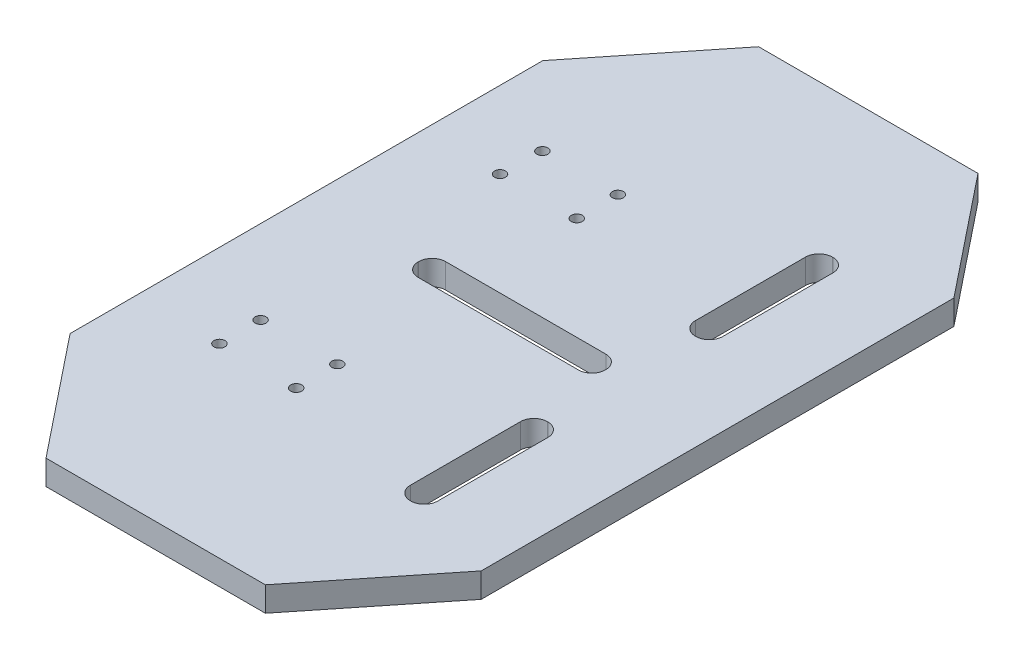
SolidWorks part; units mm, degrees
material "ABS"
ref_plane "Front Plane" through (0, 0, 0) normal (0, 0, 1) x (1, 0, 0)
ref_plane "Top Plane" through (0, 0, 0) normal (0, 1, 0) x (1, 0, 0)
ref_plane "Right Plane" through (0, 0, 0) normal (1, 0, 0) x (0, 0, -1)
other "Center of Mass"
sketch "Sketch1" plane through (0, 0, 0) normal (0, 1, 0) x (1, 0, 0)
  line L0 (-37.5, -43.1177) -> (-20.0119, -65)
  line L1 (-20.0119, -65) -> (20.0119, -65)
  line L2 (-37.5, -43.1177) -> (-37.5, 43.1177)
  line L3 (-20.0119, 65) -> (20.0119, 65)
  line L4 (37.5, -43.1177) -> (37.5, 43.1177)
  line L5 (-30.8066, -51.493) -> (30.8066, 51.493) construction
  line L6 (-32.7951, 49.0048) -> (32.7951, -49.0048) construction
  line L7 (-114.8204, 0) -> (150.9847, 0) construction
  line L8 (0, -72.5189) -> (0, 84.1411) construction
  line L9 (37.5, -43.1177) -> (20.0119, -65)
  line L10 (37.5, 43.1177) -> (20.0119, 65)
  line L11 (-37.5, 43.1177) -> (-20.0119, 65)
  point P0 (0, 0)
  dimension "D1" = 75
  dimension "D2" = 130
  dimension "D3" = 40.0238
  dimension "D4" = 86.2354
extrude "Boss-Extrude1" add sketch "Sketch1" along normal blind 4.5
sketch "Sketch5" plane through (0, 4.5, 0) normal (0, 1, 0) x (1, 0, 0)
  line L0 (-100.8141, 0) -> (111.641, 0) construction
  line L1 (20, 65) -> (20, -65) construction
  line L2 (-14.6202, -2.5) -> (14.6202, -2.5)
  line L3 (-17.0702, -0.05) -> (-17.0702, 0.05)
  line L4 (-14.6202, 2.5) -> (14.6202, 2.5)
  line L5 (17.0702, -0.05) -> (17.0702, 0.05)
  line L6 (-17.0702, -2.5) -> (17.0702, 2.5) construction
  line L7 (-17.0702, 2.5) -> (17.0702, -2.5) construction
  line L8 (20.0119, 65) -> (-20.0119, 65) construction
  line L9 (-20.0119, -65) -> (20.0119, -65) construction
  line L10 (20, 65) -> (20, 0) construction
  line L11 (20, 0) -> (20, -65) construction
  line L12 (19.95, -38.5) -> (20.05, -38.5)
  line L13 (19.95, 13.5) -> (20.05, 13.5)
  line L14 (17.5, 15.95) -> (17.5, 36.05)
  line L15 (19.95, 38.5) -> (20.05, 38.5)
  line L16 (22.5, 15.95) -> (22.5, 36.05)
  line L17 (17.5, 13.5) -> (22.5, 38.5) construction
  line L18 (17.5, 38.5) -> (22.5, 13.5) construction
  line L19 (17.5, -15.95) -> (17.5, -36.05)
  line L20 (19.95, -13.5) -> (20.05, -13.5)
  line L21 (22.5, -15.95) -> (22.5, -36.05)
  line L22 (37.5, -43.1177) -> (37.5, 43.1177) construction
  arc A0 (19.95, -38.5) -> (17.5, -36.05) centre (19.95, -36.05) cw
  arc A1 (20.05, -38.5) -> (22.5, -36.05) centre (20.05, -36.05) ccw
  arc A2 (17.5, -15.95) -> (19.95, -13.5) centre (19.95, -15.95) cw
  arc A3 (20.05, -13.5) -> (22.5, -15.95) centre (20.05, -15.95) cw
  arc A4 (-14.6202, -2.5) -> (-17.0702, -0.05) centre (-14.6202, -0.05) cw
  arc A5 (-17.0702, 0.05) -> (-14.6202, 2.5) centre (-14.6202, 0.05) cw
  arc A6 (14.6202, 2.5) -> (17.0702, 0.05) centre (14.6202, 0.05) cw
  arc A7 (14.6202, -2.5) -> (17.0702, -0.05) centre (14.6202, -0.05) ccw
  arc A8 (20.05, 13.5) -> (22.5, 15.95) centre (20.05, 15.95) ccw
  arc A9 (19.95, 13.5) -> (17.5, 15.95) centre (19.95, 15.95) cw
  arc A10 (17.5, 36.05) -> (19.95, 38.5) centre (19.95, 36.05) cw
  arc A11 (20.05, 38.5) -> (22.5, 36.05) centre (20.05, 36.05) cw
  point P3 (0, 0)
  point P14 (20, 0)
  point P15 (20, 26)
  point P17 (20, -26)
  point P18 (20, 26)
  point P31 (17.5, -38.5)
  point P34 (22.5, -38.5)
  point P37 (17.5, -13.5)
  point P40 (22.5, -13.5)
  dimension "D7" = 2.45
  dimension "D1" = 5
  dimension "D2" = 26
  dimension "D3" = 26
  dimension "D4" = 5
  dimension "D5" = 25
  dimension "D6" = 15
extrude "Cut-Extrude2" cut sketch "Sketch5" against normal blind 10
sketch "Sketch7" plane through (0, 4.5, 0) normal (0, 1, 0) x (1, 0, 0)
  line L0 (-37.5, 43.1177) -> (-37.5, -43.1177) construction
  line L1 (20.0119, 65) -> (-20.0119, 65) construction
  line L2 (-20.0119, -65) -> (20.0119, -65) construction
  line L4 (-30.476, 17.035) -> (-30.476, 35.535)
  line L5 (-2.476, 17.035) -> (-30.476, 17.035)
  line L6 (-2.476, 35.535) -> (-30.476, 35.535)
  line L7 (-2.476, 17.035) -> (-2.476, 35.535)
  line L11 (-16.476, 43.5449) -> (-16.476, 10.5144) construction
  line L12 (-23.476, 43.5449) -> (-23.476, 10.5144) construction
  line L13 (-23.2436, 32.535) -> (-23.2436, 25.035) construction
  line L14 (-23.7676, 28.785) -> (4.2324, 28.785) construction
  circle A0 centre (-23.2436, 28.79) radius 1
  circle A1 centre (-9.476, 28.79) radius 1
  circle A2 centre (-23.476, 21.29) radius 1
  circle A3 centre (-9.476, 21.29) radius 1
  circle A4 centre (-8.27, -23.6) radius 1
  circle A5 centre (-22.27, -23.6) radius 1
  circle A6 centre (-8.27, -31.1) radius 1
  circle A7 centre (-22.27, -31.1) radius 1
  circle A8 centre (-9.476, 28.79) radius 2
  circle A9 centre (-9.476, 21.29) radius 2
  circle A10 centre (-23.476, 21.29) radius 2
  circle A11 centre (-23.2436, 28.79) radius 2
  circle A12 centre (-22.27, -31.1) radius 2
  circle A13 centre (-22.27, -23.6) radius 2
  circle A14 centre (-8.27, -23.6) radius 2
  circle A15 centre (-8.27, -31.1) radius 2
  point P12 (-16.7676, 25.035)
  point P17 (-23.476, 28.79)
  dimension "D5" = 2
  dimension "D22" = 2
  dimension "D23" = 2
  dimension "D24" = 2
  dimension "D25" = 2
  dimension "D26" = 4
  dimension "D27" = 4
  dimension "D28" = 4
  dimension "D29" = 4
  dimension "D30" = 4
  dimension "D31" = 4
  dimension "D32" = 4
  dimension "D33" = 4
  dimension "D2" = 7
  dimension "D3" = 14
  dimension "D4" = 33.9
  dimension "D6" = 28
  dimension "D7" = 7.024
  dimension "D8" = 14
  dimension "D9" = 14
  dimension "D10" = 7.5
  dimension "D11" = 7.5
  dimension "D12" = 7
  dimension "D13" = 0.2324
  dimension "D14" = 28.785
  dimension "D15" = 28
  dimension "D16" = 36.21
  dimension "D17" = 36.21
  dimension "D18" = 36.21
  dimension "D19" = 7.5
  dimension "D20" = 33.9
  dimension "D21" = 7.5
  dimension "D34" = 15.23
  dimension "D35" = 15.23
  dimension "D36" = 14
  dimension "D37" = 14
extrude "Cut-Extrude3" cut sketch "Sketch7" against normal blind 5 contours A3 | A2 | A0 | A5 | A7 | A6 | A4 | A1
sketch "Sketch8" plane through (0, 4.5, 0) normal (0, 1, 0) x (1, 0, 0)
  line L1 (-37.5, 43.1177) -> (-37.5, -43.1177) construction
  line L3 (-20.0119, -65) -> (20.0119, -65) construction
  circle A1 centre (-8.27, -31.1) radius 1 construction
  circle A2 centre (-22.27, -23.6) radius 1 construction
  circle A4 centre (-9.476, 28.79) radius 2
  circle A5 centre (-9.476, 21.29) radius 2
  circle A6 centre (-23.476, 21.29) radius 2
  circle A7 centre (-23.2436, 28.79) radius 2
  dimension "D1" = 33.9
  dimension "D2" = 15.23
  dimension "D3" = 14.024
  dimension "D5" = 4
  dimension "D6" = 4
  dimension "D7" = 4
  dimension "D8" = 4
sketch "Sketch11" plane through (0, 0, 0) normal (0, -1, 0) x (1, 0, 0)
  circle A0 centre (-8.27, 31.1) radius 2
  circle A1 centre (-8.27, 23.6) radius 2
  circle A2 centre (-22.27, 31.1) radius 2
  circle A3 centre (-22.27, 23.6) radius 2
  circle A4 centre (-9.476, -21.29) radius 2
  circle A5 centre (-9.476, -28.79) radius 2
  circle A6 centre (-23.476, -21.29) radius 2
  circle A7 centre (-23.2436, -28.79) radius 2
  circle M2 centre (-9.476, -21.29) radius 1
  circle M36 centre (-22.27, 23.6) radius 1
  circle M39 centre (-8.27, 23.6) radius 1
  circle M40 centre (-9.476, -28.79) radius 1
  dimension "D1" = 4
  dimension "D2" = 4
  dimension "D3" = 4
  dimension "D4" = 4
  dimension "D5" = 4
  dimension "D6" = 4
  dimension "D7" = 4
  dimension "D8" = 4
extrude "Cut-Extrude4" cut sketch "Sketch11" against normal blind 1.65 contours A1 M39 | A3 M36 | A4 M2 | A5 M40 | A0 | A2 | A7 | A6
